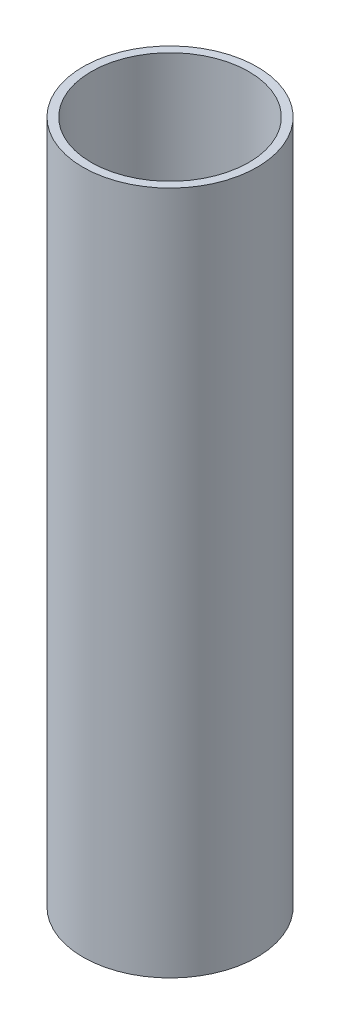
SolidWorks part; units mm, degrees
ref_plane "Front Plane" through (0, 0, 0) normal (0, 0, 1) x (1, 0, 0)
ref_plane "Top Plane" through (0, 0, 0) normal (0, 1, 0) x (1, 0, 0)
ref_plane "Right Plane" through (0, 0, 0) normal (1, 0, 0) x (0, 0, -1)
sketch "Sketch1" plane through (0, 0, 0) normal (0, 1, 0) x (1, 0, 0)
  circle A0 centre (0, 0) radius 21
  circle A1 centre (0, 0) radius 19
extrude "Boss-Extrude1" add sketch "Sketch1" along normal blind 165
